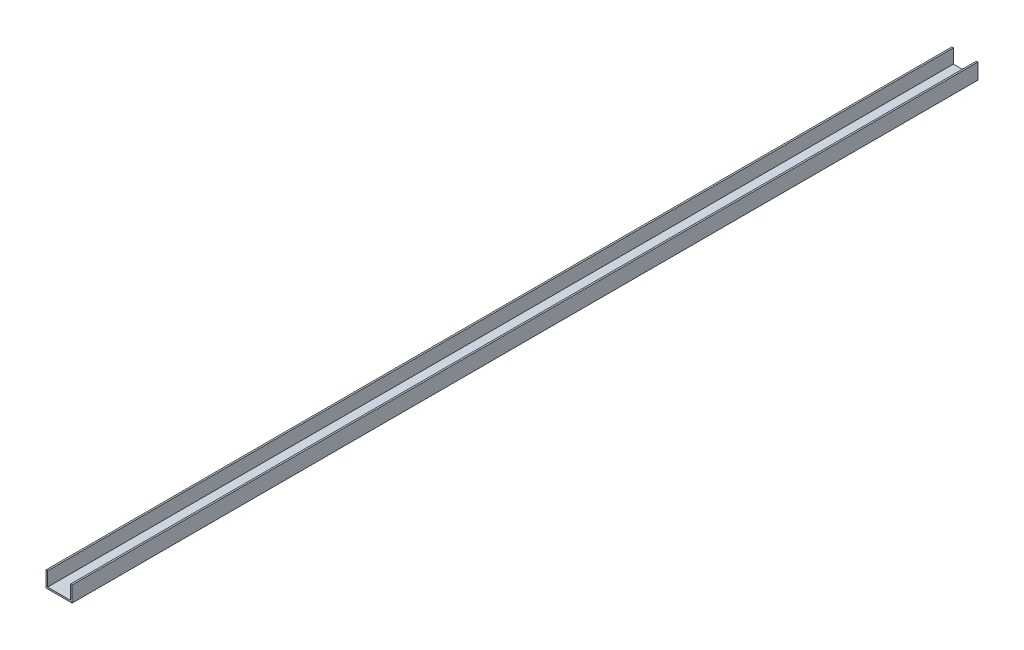
SolidWorks part; units mm, degrees
material "ASTM A36 Steel"
ref_plane "Front Plane" through (0, 0, 0) normal (0, 0, 1) x (1, 0, 0)
ref_plane "Top Plane" through (0, 0, 0) normal (0, 1, 0) x (1, 0, 0)
ref_plane "Right Plane" through (0, 0, 0) normal (1, 0, 0) x (0, 0, -1)
sketch "Sketch1" plane through (0, 0, 0) normal (0, 0, 1) x (1, 0, 0)
  line L0 (-25, 0) -> (25, 0)
  line L1 (25, 0) -> (25, 30)
  line L2 (-25, 0) -> (-25, 30)
  line L3 (-22, 3) -> (-22, 30)
  line L4 (-22, 3) -> (22, 3)
  line L5 (22, 3) -> (22, 30)
  line L6 (-25, 30) -> (-22, 30)
  line L7 (22, 30) -> (25, 30)
  point P4 (0, 0)
  dimension "D1" = 30
  dimension "D2" = 50
  dimension "D3" = 3
extrude "Boss-Extrude1" add sketch "Sketch1" along normal blind 1732
